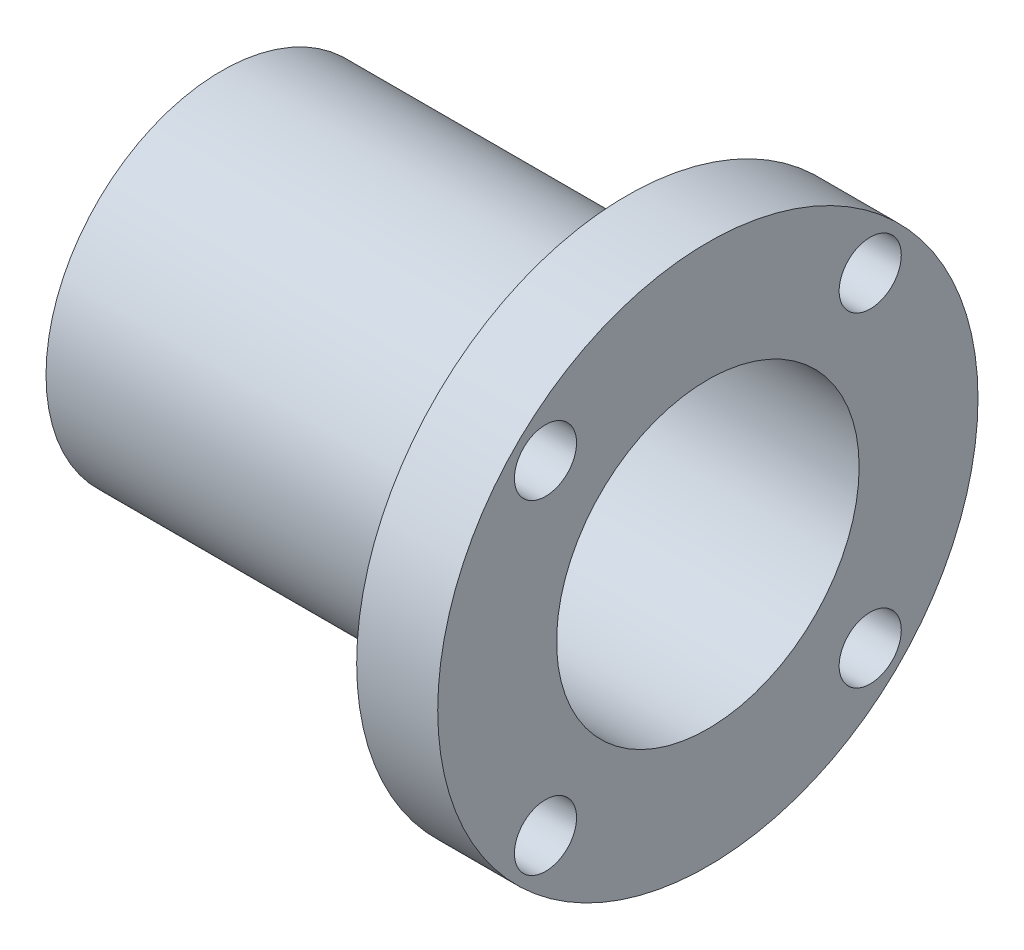
SolidWorks part; units mm, degrees
ref_plane "Front Plane" through (0, 0, 0) normal (0, 0, 1) x (1, 0, 0)
ref_plane "Top Plane" through (0, 0, 0) normal (0, 1, 0) x (1, 0, 0)
ref_plane "Right Plane" through (0, 0, 0) normal (1, 0, 0) x (0, 0, -1)
sketch "Sketch2" plane through (0, 0, 0) normal (1, 0, 0) x (0, 0, -1)
  circle A0 centre (0, 0) radius 10
  dimension "D1" = 20
extrude "Boss-Extrude1" add sketch "Sketch2" along normal blind 3 separate body
sketch "Sketch3" plane through (0, 0, 0) normal (1, 0, 0) x (0, 0, -1)
  circle A0 centre (0, 0) radius 6.5
  circle A1 centre (0, 0) radius 5.6
  dimension "D1" = 13
  dimension "D2" = 11.2
extrude "Boss-Extrude2" add sketch "Sketch3" against normal blind 15
sketch "Sketch4" plane through (0, 0, 0) normal (1, 0, 0) x (0, 0, -1)
  circle A0 centre (0, 0) radius 6.5
  circle A1 centre (0, 0) radius 2.095
  dimension "D1" = 13
  dimension "D2" = 4.19
extrude "Boss-Extrude3" add sketch "Sketch4" along normal blind 3 from surface at -15 starting at face at (-15, 0, -5.6)
sketch "Sketch5" plane through (0, 0, 0) normal (1, 0, 0) x (0, 0, -1)
  circle A0 centre (0, 0) radius 5.6
  dimension "D1" = 11.2
extrude "Cut-Extrude1" cut sketch "Sketch5" along normal blind 3
sketch "Sketch6" plane through (0, 0, 0) normal (1, 0, 0) x (0, 0, -1)
  line L0 (0, 0) -> (0, 10) construction
  line L1 (0, 0) -> (10, 0) construction
  line L2 (0, 0) -> (7.0711, 7.0711) construction
  circle A0 centre (0, 0) radius 10 construction
  circle A1 centre (0, 0) radius 8.5 construction
  circle A2 centre (6.0104, 6.0104) radius 1.15
  circle A3 centre (6.0104, -6.0104) radius 1.15
  circle A4 centre (-6.0104, -6.0104) radius 1.15
  circle A5 centre (-6.0104, 6.0104) radius 1.15
  point P20 (0, 0)
  dimension "D2" = 17
  dimension "D3" = 2.3
  dimension "D1" = 45
  dimension "D4" = 4
extrude "Cut-Extrude2" cut sketch "Sketch6" along normal through all
